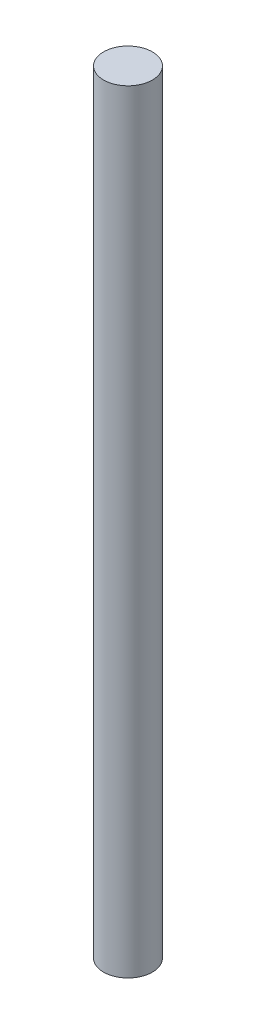
SolidWorks part; units mm, degrees
ref_plane "Front Plane" through (0, 0, 0) normal (0, 0, 1) x (1, 0, 0)
ref_plane "Top Plane" through (0, 0, 0) normal (0, 1, 0) x (1, 0, 0)
ref_plane "Right Plane" through (0, 0, 0) normal (1, 0, 0) x (0, 0, -1)
sketch "Sketch1" plane through (0, 0, 0) normal (0, 1, 0) x (1, 0, 0)
  circle A0 centre (0, 0) radius 914.4
  dimension "D1" = 1828.8
extrude "Boss-Extrude1" add sketch "Sketch1" along normal blind 28956
